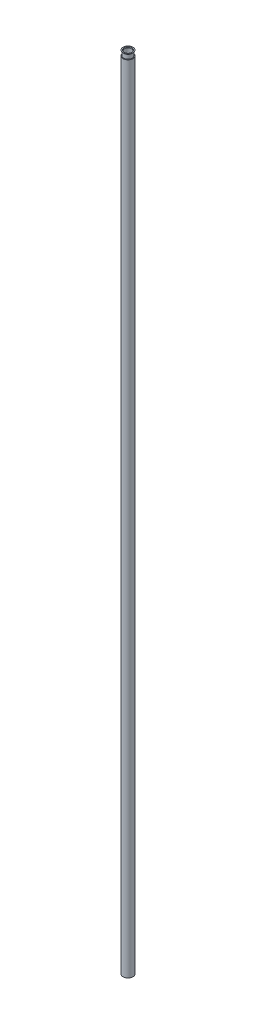
SolidWorks part; units mm, degrees
ref_plane "Alzado" through (0, 0, 0) normal (0, 0, 1) x (1, 0, 0)
ref_plane "Planta" through (0, 0, 0) normal (0, 1, 0) x (1, 0, 0)
ref_plane "Vista lateral" through (0, 0, 0) normal (1, 0, 0) x (0, 0, -1)
sketch "Croquis1" plane through (0, 0, 0) normal (0, 1, 0) x (1, 0, 0)
  circle A0 centre (0, 0) radius 5
  dimension "10" = 10
extrude "Saliente-Extruir1" add sketch "Croquis1" along normal blind 800
sketch "Croquis2" plane through (0, 0, 0) normal (0, -1, 0) x (1, 0, 0)
  circle A0 centre (0, 0) radius 3.5
  dimension "D1" = 7
extrude "Cortar-Extruir1" cut sketch "Croquis2" against normal through all contours A0
sketch "Croquis3" plane through (0, 800, 0) normal (0, 1, 0) x (1, 0, 0)
  circle A0 centre (0, 0) radius 6
  dimension "D1" = 12
extrude "Saliente-Extruir2" add sketch "Croquis3" along normal blind 1
sketch "Croquis4" plane through (0, 801, 0) normal (0, 1, 0) x (1, 0, 0)
  circle A0 centre (0, 0) radius 3.5
  dimension "D1" = 7
extrude "Cortar-Extruir3" cut sketch "Croquis4" against normal blind 1
chamfer "Chaflán1" distance 1 angle 45 1 edges at (0, 801, 3.5)
sketch "Croquis5" plane through (0, 0, 0) normal (0, 0, 1) x (1, 0, 0)
  line L1 (-6.3495, 800) -> (7.0184, 800)
  line L2 (-6.3495, 800) -> (-6.3495, 801.6878)
  line L3 (-6.3495, 801.6878) -> (7.0184, 801.6878)
  line L4 (7.0184, 800) -> (7.0184, 801.6878)
extrude "Cortar-Extruir4" cut sketch "Croquis5" against normal through all both and the other way through all
sketch "Croquis6" plane through (0, 0, 0) normal (0, 0, 1) x (1, 0, 0)
  line L0 (0, 810.0312) -> (0, 792.9112) construction
  line L1 (-3.5, 800) -> (-3.5, 804.5)
  line L2 (-4, 805) -> (-5, 805)
  line L3 (-5, 805) -> (-4.26, 804.25)
  line L4 (-4.26, 804.25) -> (-4.26, 800)
  line L5 (5, 800) -> (-5, 800) construction
  line L6 (-3.5, 804.5) -> (-4, 805)
  line L7 (-3.5, 800) -> (-4.26, 800)
  point P4 (-3.5, 805)
  dimension "D1" = 5
  dimension "D2" = 4.25
  dimension "D3" = 4.26
revolve "Revolución1" add sketch "Croquis6" angle 360 about L0
